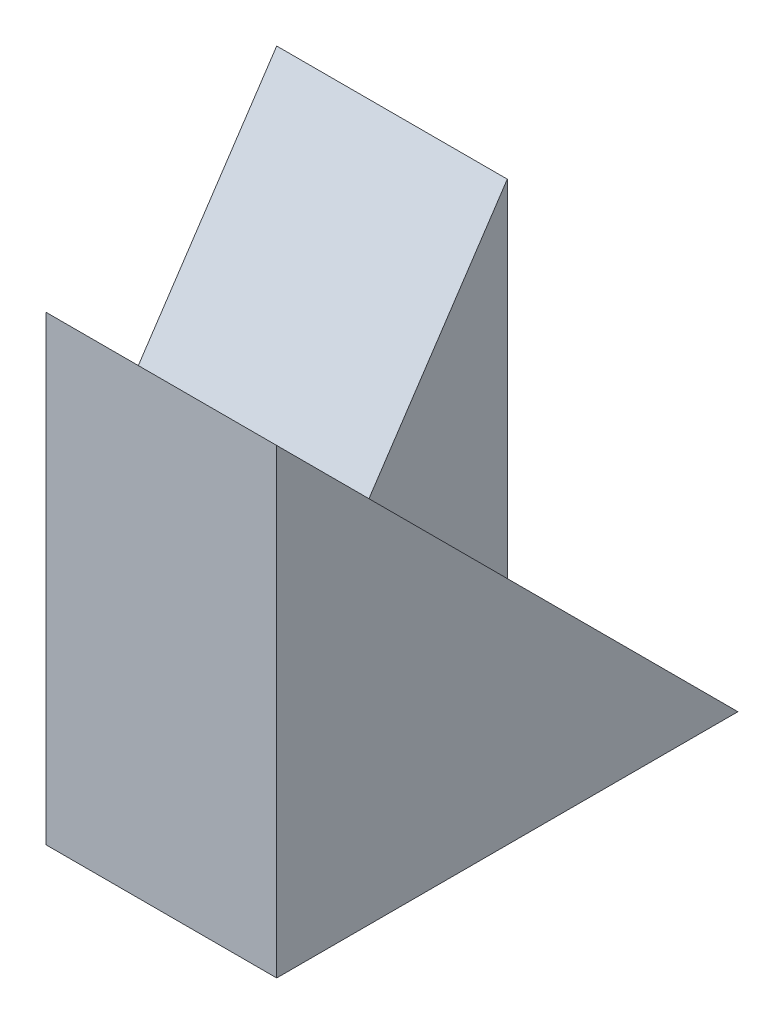
SolidWorks part; units mm, degrees
ref_plane "Front Plane" through (0, 0, 0) normal (0, 0, 1) x (1, 0, 0)
ref_plane "Top Plane" through (0, 0, 0) normal (0, 1, 0) x (1, 0, 0)
ref_plane "Right Plane" through (0, 0, 0) normal (1, 0, 0) x (0, 0, -1)
sketch "Sketch1" plane through (0, 0, 0) normal (1, 0, 0) x (0, 0, -1)
  line L1 (0, 0) -> (4, 0)
  line L2 (0, 0) -> (0, 4)
  line L3 (0, 4) -> (4, 4)
  line L4 (4, 0) -> (4, 4)
  dimension "D1" = 4
  dimension "D2" = 4
extrude "Boss-Extrude1" add sketch "Sketch1" along normal blind 2
sketch "Sketch2" plane through (0, 0, 0) normal (-1, 0, 0) x (0, 0, 1)
  line L1 (-4, 0) -> (-2, 0)
  line L2 (-4, 0) -> (-4, 3)
  line L3 (-4, 3) -> (-2, 3)
  line L4 (-2, 0) -> (-2, 3)
  dimension "D1" = 3
  dimension "D2" = 2
extrude "Boss-Extrude2" add sketch "Sketch2" along normal blind 2
sketch "Sketch3" plane through (2, 0, 0) normal (1, 0, 0) x (0, 0, -1)
  line L0 (0, 4) -> (4, 0)
  line L1 (4, 0) -> (4, 4)
  line L2 (4, 0) -> (4, 4) construction
  line L3 (4, 4) -> (0, 4) construction
  line L4 (4, 4) -> (0, 4)
extrude "Cut-Extrude2" cut sketch "Sketch3" against normal blind 2
sketch "Sketch4" plane through (-2, 0, 0) normal (-1, 0, 0) x (0, 0, 1)
  line L0 (-2, 0) -> (-4, 3)
  line L1 (-4, 3) -> (-2, 3)
  line L2 (-2, 3) -> (-2, 0)
extrude "Cut-Extrude3" cut sketch "Sketch4" against normal blind 2
